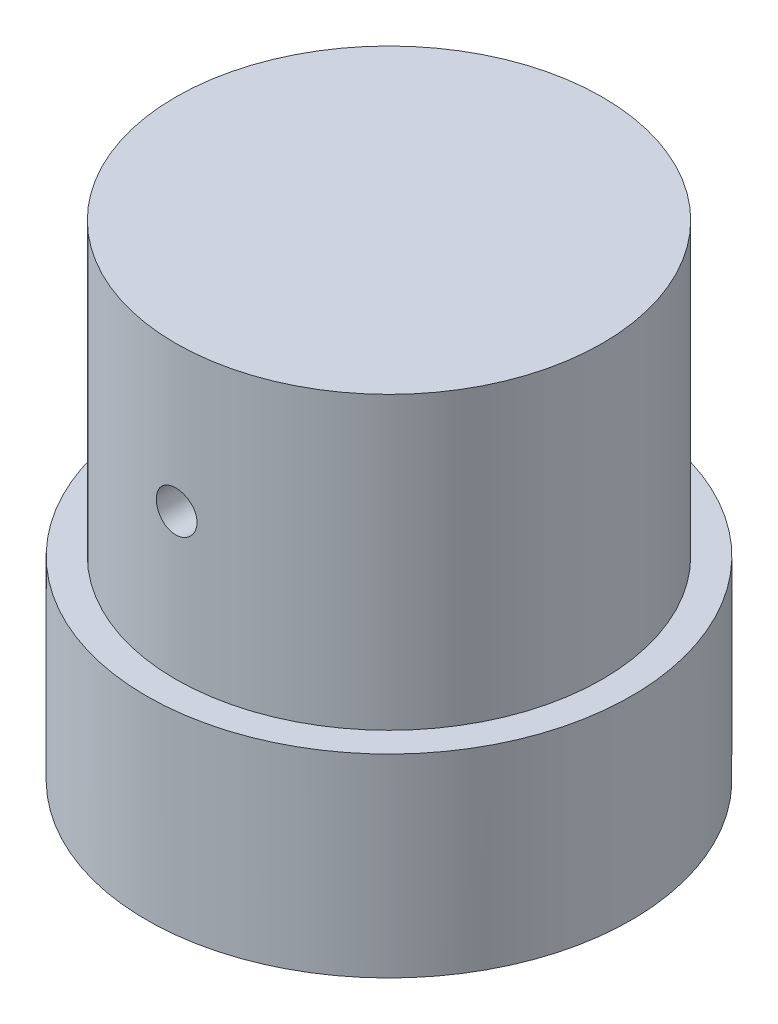
SolidWorks part; units mm, degrees
material "Náilon 101"
ref_plane "Plano frontal" through (0, 0, 0) normal (0, 0, 1) x (1, 0, 0)
ref_plane "Plano superior" through (0, 0, 0) normal (0, 1, 0) x (1, 0, 0)
ref_plane "Plano direito" through (0, 0, 0) normal (1, 0, 0) x (0, 0, -1)
sketch "Esboço1" plane through (0, 0, 0) normal (0, 1, 0) x (1, 0, 0)
  circle A0 centre (0, 0) radius 22
  dimension "D1" = 44
extrude "Ressalto-extrusão1" add sketch "Esboço1" along normal blind 30
sketch "Esboço2" plane through (0, 0, 0) normal (0, -1, 0) x (1, 0, 0)
  line L5 (-25.8, -25.8) -> (25.8, -25.8)
  line L6 (-25.8, -25.8) -> (-25.8, 25.8)
  line L7 (-25.8, 25.8) -> (25.8, 25.8)
  line L8 (25.8, -25.8) -> (25.8, 25.8)
  line L9 (-25.8, -25.8) -> (25.8, 25.8) construction
  line L10 (-25.8, 25.8) -> (25.8, -25.8) construction
  point P0 (0, 0)
  point P1 (0, 0)
  dimension "D1" = 51.6
  dimension "D2" = 51.6
extrude "Ressalto-extrusão2" add sketch "Esboço2" along normal blind 20
sketch "Esboço4" plane through (25.8, 0, 0) normal (1, 0, 0) x (0, 0, -1)
  line L0 (25.8, -20) -> (-25.8, -20) construction
  line L1 (25.8, -20) -> (25.8, 0) construction
  circle A0 centre (0, -10) radius 5
  point P5 (0, -20)
  point P9 (25.8, -10)
  dimension "D1" = 10
extrude "Corte-extrusão2" [suppressed] cut sketch "Esboço4" against normal through all
sketch "Esboço5" plane through (0, 30, 0) normal (0, 1, 0) x (1, 0, 0)
  circle A0 centre (0, 0) radius 5
  dimension "D1" = 10
extrude "Corte-extrusão3" [suppressed] cut sketch "Esboço5" against normal through all
sketch "Esboço8" plane through (0, 0, 25.8) normal (0, 0, 1) x (1, 0, 0)
  line L0 (0, 0) -> (0, 30) construction
  line L1 (22, 30) -> (-22, 30) construction
  circle A0 centre (0, 15) radius 2.5
  dimension "D1" = 5
hole_wizard "Broca de rosquear para tarraxa de M52" positions "Esboço11" profile "Esboço13" hole size "M5" standard "ISO"
sketch "Esboço11" plane through (0, 0, 25.8) normal (0, 0, 1) x (1, 0, 0)
  point P0 (0, 15)
sketch "Esboço13" plane through (0, 15, 25.8) normal (1, 0, 0) x (0, -1, 0)
  line L0 (0, 0) -> (0, 16.2618)
  line L1 (0, 16.2618) -> (2.1, 15)
  line L2 (2.1, 15) -> (2.1, 0)
  line L5 (2.1, 0) -> (0, 0)
  line L10 (0, 16.2618) -> (-2.1, 15) construction
  line L11 (0, -6.35) -> (0, 107.95) construction
  dimension "Hole Dia." = 4.2
  dimension "Hole Depth" = 15
  dimension "Drill Angle" = 118
mirror "Espelhar1" about plane through (0, 0, 0) normal (0, 0, 1) of "Broca de rosquear para tarraxa de M52"
sketch "Esboço14" plane through (-25.8, 0, 0) normal (-1, 0, 0) x (0, 0, 1)
  line L0 (0, 0) -> (0, 30) construction
  line L1 (25.8, 0) -> (-25.8, 0) construction
  line L2 (22, 30) -> (-22, 30) construction
hole_wizard "Broca de rosquear para tarraxa de M53" [suppressed] positions "Esboço15" profile "Esboço16" hole size "M5" standard "ISO"
sketch "Esboço15" plane through (-25.8, 0, 0) normal (-1, 0, 0) x (0, 0, 1)
  line L0 (0, 0) -> (0, 30) construction
  point P0 (0, 15)
sketch "Esboço16" plane through (-25.8, 15, 0) normal (0, 1, 0) x (0, 0, 1)
  line L0 (0, 0) -> (0, 16.2618)
  line L1 (0, 16.2618) -> (2.1, 15)
  line L2 (2.1, 15) -> (2.1, 0)
  line L5 (2.1, 0) -> (0, 0)
  line L10 (0, 16.2618) -> (-2.1, 15) construction
  line L11 (0, -6.35) -> (0, 107.95) construction
  dimension "Hole Dia." = 4.2
  dimension "Hole Depth" = 15
  dimension "Drill Angle" = 118
mirror "Espelhar2" [suppressed] about plane through (0, 0, 0) normal (1, 0, 0)
sketch "Esboço17" plane through (0, -20, 0) normal (0, -1, 0) x (1, 0, 0)
  line L4 (25.8, -25.8) -> (25.8, 25.8)
  line L5 (25.8, 25.8) -> (-25.8, 25.8)
  line L6 (-25.8, 25.8) -> (-25.8, -25.8)
  line L7 (-25.8, -25.8) -> (25.8, -25.8)
  line L8 (25.8, -25.8) -> (25.8, 25.8)
  line L9 (25.8, 25.8) -> (-25.8, 25.8)
  line L10 (-25.8, 25.8) -> (-25.8, -25.8)
  line L11 (-25.8, -25.8) -> (25.8, -25.8)
  circle A0 centre (0, 0) radius 25
  dimension "D1" = 50
  dimension "D2" = 0
extrude "Corte-extrusão4" cut sketch "Esboço17" against normal up to next
sketch "Esboço18" plane through (0, -20, 0) normal (0, -1, 0) x (1, 0, 0)
  line L0 (0, -25) -> (0, 25) construction
  line L1 (-25, 0) -> (25, 0) construction
  line L2 (0, 0) -> (17.6777, 17.6777) construction
  circle A0 centre (0, 0) radius 25 construction
  circle A1 centre (8.8388, 8.8388) radius 2.5
  circle A2 centre (-8.8388, 8.8388) radius 2.5
  circle A3 centre (8.8388, -8.8388) radius 2.5
  circle A4 centre (-8.8388, -8.8388) radius 2.5
  dimension "D1" = 5
extrude "Corte-extrusão5" cut sketch "Esboço18" against normal blind 15
